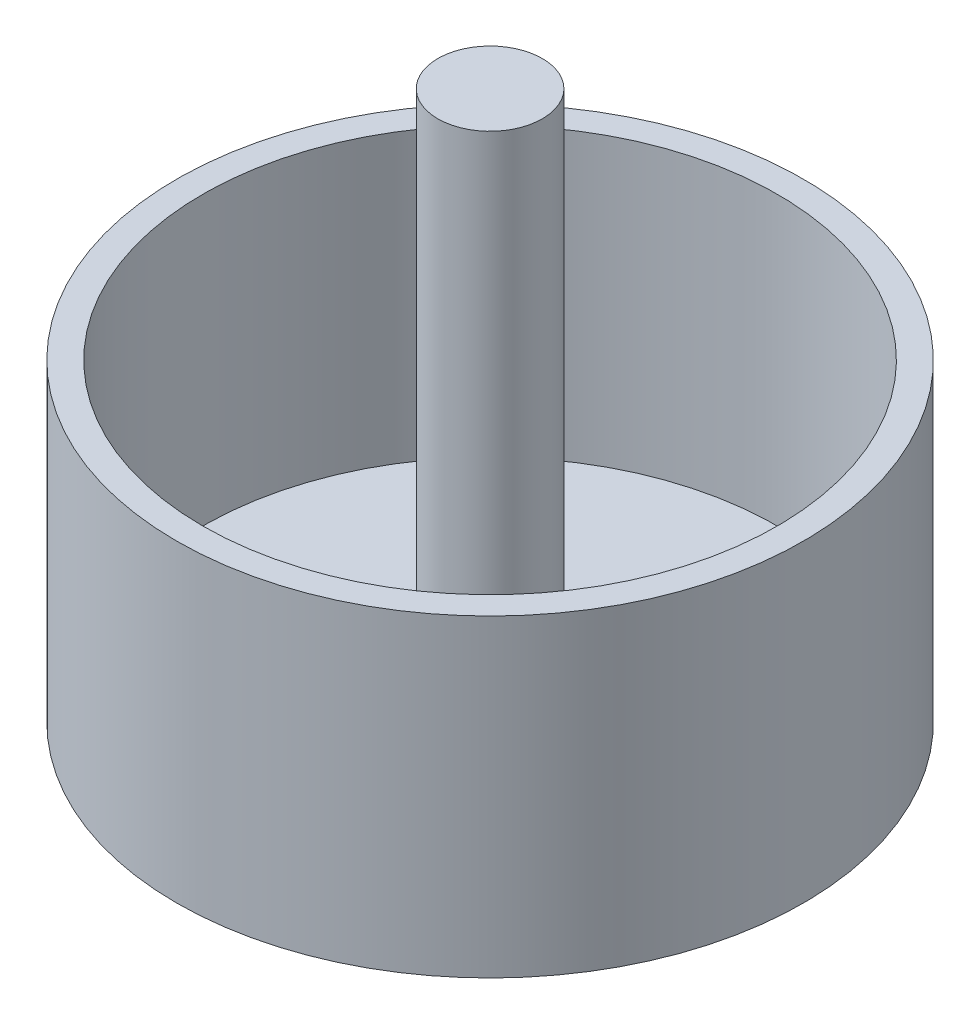
SolidWorks part; units mm, degrees
material "6061 Alloy"
ref_plane "Front Plane" through (0, 0, 0) normal (0, 0, 1) x (1, 0, 0)
ref_plane "Top Plane" through (0, 0, 0) normal (0, 1, 0) x (1, 0, 0)
ref_plane "Right Plane" through (0, 0, 0) normal (1, 0, 0) x (0, 0, -1)
sketch "Sketch1" plane through (0, 0, 0) normal (0, 1, 0) x (1, 0, 0)
  circle A0 centre (0, 0) radius 76.2
  dimension "D1" = 152.4
extrude "Boss-Extrude1" add sketch "Sketch1" along normal blind 76.2
sketch "Sketch2" plane through (0, 76.2, 0) normal (0, 1, 0) x (1, 0, 0)
  circle A0 centre (0, 0) radius 12.7
  dimension "D1" = 25.4
extrude "Boss-Extrude2" add sketch "Sketch2" along normal blind 57.15
sketch "Sketch3" plane through (0, 76.2, 0) normal (0, 1, 0) x (1, 0, 0)
  circle A2 centre (0, 0) radius 69.85
  circle A3 centre (0, 0) radius 69.85
  circle A4 centre (0, 0) radius 12.7
  dimension "D1" = 6.35
extrude "Cut-Extrude1" cut sketch "Sketch3" against normal blind 69.85
